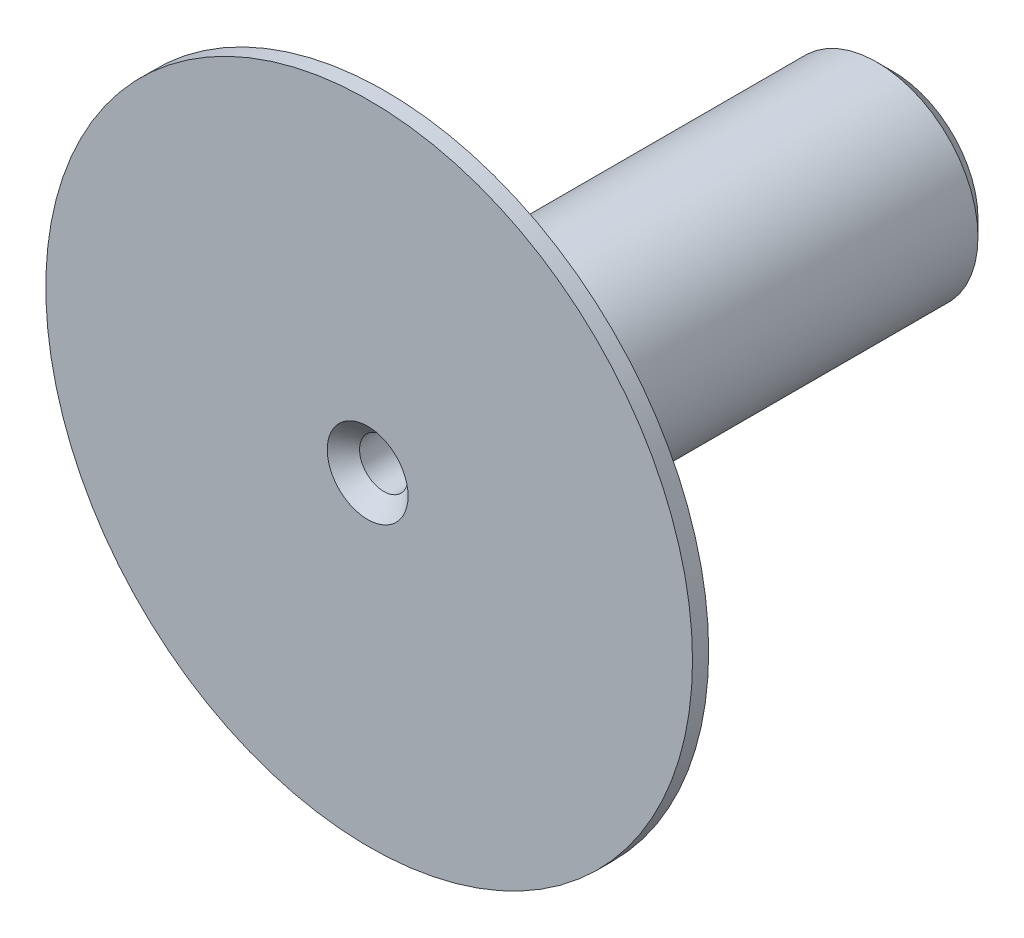
SolidWorks part; units mm, degrees
ref_plane "Front Plane" through (0, 0, 0) normal (0, 0, 1) x (1, 0, 0)
ref_plane "Top Plane" through (0, 0, 0) normal (0, 1, 0) x (1, 0, 0)
ref_plane "Right Plane" through (0, 0, 0) normal (1, 0, 0) x (0, 0, -1)
sketch "Sketch1" plane through (0, 0, 0) normal (0, 0, 1) x (1, 0, 0)
  circle A0 centre (0, 0) radius 0.3
  circle A1 centre (0, 0) radius 1.25
  dimension "D1" = 2.5
  dimension "D2" = 0.6
extrude "Boss-Extrude1" add sketch "Sketch1" along normal blind 6.5
sketch "Sketch2" plane through (0, 0, 6.5) normal (0, 0, 1) x (1, 0, 0)
  circle A0 centre (0, 0) radius 1.25
  circle A1 centre (0.0187, 0) radius 4
  circle A2 centre (0, 0) radius 1.25 construction
  dimension "D1" = 8
extrude "Boss-Extrude2" add sketch "Sketch2" against normal blind 0.2
chamfer "Chamfer1" distance 0.2 angle 45 3 edges at (1.25, 0, 0) (0.3, 0, 0) (0.3, 0, 6.5)
